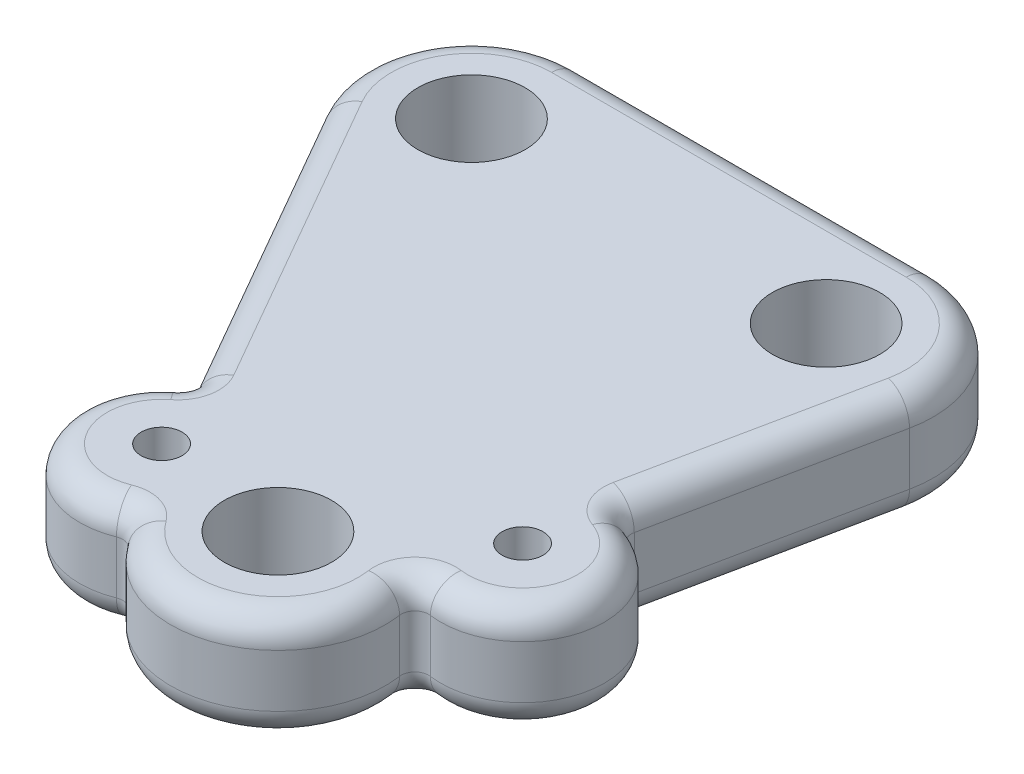
SolidWorks part; units mm, degrees
ref_plane "Front Plane" through (0, 0, 0) normal (0, 0, 1) x (1, 0, 0)
ref_plane "Top Plane" through (0, 0, 0) normal (0, 1, 0) x (1, 0, 0)
ref_plane "Right Plane" through (0, 0, 0) normal (1, 0, 0) x (0, 0, -1)
sketch "Sketch1" plane through (0, 0, 0) normal (0, 1, 0) x (1, 0, 0)
  line L0 (-41.6934, -4.9772) -> (-25.015, -34.0417)
  line L1 (5.1565, -24.4129) -> (9.7922, -2.0279)
  line L2 (-33.02, 10) -> (0, 10)
  line L3 (-8.7564, -42.2828) -> (0, 0) construction
  line L4 (0, 0) -> (-33.02, 0) construction
  line L5 (-33.02, 0) -> (-8.7564, -42.2828) construction
  line L6 (-21.2224, -40.6509) -> (-12.549, -35.6737) construction
  line L7 (3.6113, -31.8746) -> (-6.181, -29.8467) construction
  arc A0 (-41.6934, -4.9772) -> (-33.02, 10) centre (-33.02, 0) cw
  arc A1 (9.7922, -2.0279) -> (0, 10) centre (0, 0) ccw
  arc A2 (-17.4298, -47.26) -> (0.653, -38.8969) centre (-8.7564, -42.2828) ccw
  circle A3 centre (-33.02, 0) radius 5
  circle A4 centre (0, 0) radius 5
  circle A5 centre (-8.7564, -42.2828) radius 5
  arc A6 (-17.4298, -47.26) -> (-25.015, -34.0417) centre (-21.2224, -40.6509) cw
  arc A7 (0.653, -38.8969) -> (5.1565, -24.4129) centre (3.6113, -31.8746) ccw
  circle A8 centre (-21.2224, -40.6509) radius 1.905
  circle A9 centre (3.6113, -31.8746) radius 1.905
  dimension "D4" = 10
  dimension "D5" = 10
  dimension "D6" = 7.62
  dimension "D7" = 7.62
  dimension "D10" = 3.81
  dimension "D11" = 3.81
  dimension "D1" = 48.75
  dimension "D2" = 33.02
  dimension "D3" = 43.18
  dimension "D8" = 7.62
  dimension "D9" = 12.7
extrude "Boss-Extrude1" add sketch "Sketch1" along normal blind 10
fillet "Fillet2" radius 1.27 4 edges at (5.1565, 5, 24.4129) (0.653, 5, 38.8969) (-17.4298, 5, 47.26) (-25.015, 5, 34.0417)
fillet "Fillet1" radius 2.54 24 edges at (-41.6737, 0, -5.0114) (-16.51, 0, -10) (7.755, 0, -6.3135) (7.5939, 0, 12.6432) (-5.0049, 0, 51.5525) (-41.6737, 10, -5.0114) (-16.51, 10, -10) (7.755, 10, -6.3135) (7.5939, 10, 12.6432) (-5.0049, 10, 51.5525) (-33.6475, 0, 18.9982) (-33.6475, 10, 18.9982) (5.5305, 0, 24.1356) (11.0089, 0, 33.7018) (1.4987, 0, 39.7862) (-17.5351, 0, 47.6703) (-27.8179, 0, 44.467) (-25.4567, 0, 33.8947) (5.5305, 10, 24.1356) (11.0089, 10, 33.7018) (1.4987, 10, 39.7862) (-17.5351, 10, 47.6703) (-27.8179, 10, 44.467) (-25.4567, 10, 33.8947)
scale "Scale1" scale about centroid uniform scaling yes scale factor 0.66
